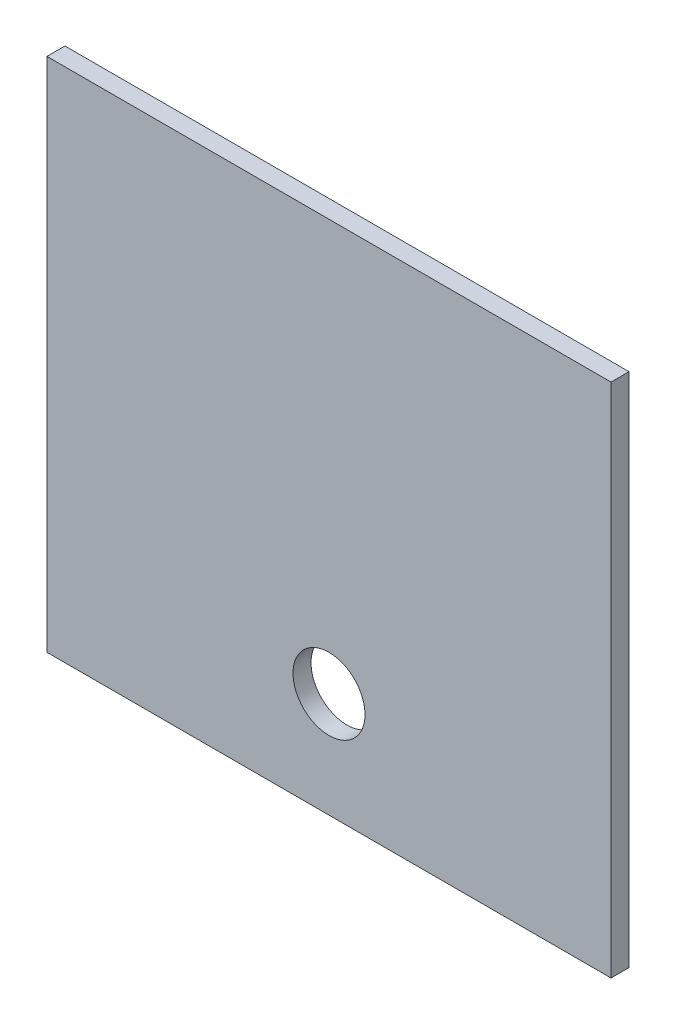
SolidWorks part; units mm, degrees
material "Oak"
ref_plane "Front Plane" through (0, 0, 0) normal (0, 0, 1) x (1, 0, 0)
ref_plane "Top Plane" through (0, 0, 0) normal (0, 1, 0) x (1, 0, 0)
ref_plane "Right Plane" through (0, 0, 0) normal (1, 0, 0) x (0, 0, -1)
sketch "Sketch1" plane through (0, 0, 0) normal (0, 0, 1) x (1, 0, 0)
  line L1 (-298.45, -152.4) -> (298.45, -152.4)
  line L2 (-298.45, -152.4) -> (-298.45, 152.4)
  line L3 (-298.45, 152.4) -> (298.45, 152.4)
  line L4 (298.45, -152.4) -> (298.45, 152.4)
  line L5 (-298.45, -152.4) -> (298.45, 152.4) construction
  line L6 (-298.45, 152.4) -> (298.45, -152.4) construction
  line L7 (-298.45, 158.75) -> (-298.45, 177.8) construction
  point P4 (0, 0)
  dimension "D2" = 304.8
extrude "Boss-Extrude1" add sketch "Sketch1" along normal blind 19.05
sketch "Sketch2" plane through (0, 152.4, 0) normal (0, 1, 0) x (1, 0, 0)
  line L4 (298.45, 0) -> (-298.45, 0)
  line L5 (-298.45, 0) -> (-298.45, -19.05)
  line L6 (-298.45, -19.05) -> (298.45, -19.05)
  line L7 (298.45, -19.05) -> (298.45, 0)
  line L8 (298.45, 0) -> (-298.45, 0)
  line L9 (-298.45, 0) -> (-298.45, -19.05)
  line L10 (-298.45, -19.05) -> (298.45, -19.05)
  line L11 (298.45, -19.05) -> (298.45, 0)
  dimension "D1" = 0
extrude "Boss-Extrude2" add sketch "Sketch2" along normal blind 25.4
sketch "Sketch3" plane through (0, -152.4, 0) normal (0, -1, 0) x (1, 0, 0)
  line L4 (-298.45, 0) -> (298.45, 0)
  line L5 (298.45, 0) -> (298.45, 19.05)
  line L6 (298.45, 19.05) -> (-298.45, 19.05)
  line L7 (-298.45, 19.05) -> (-298.45, 0)
  line L8 (-298.45, 0) -> (298.45, 0)
  line L9 (298.45, 0) -> (298.45, 19.05)
  line L10 (298.45, 19.05) -> (-298.45, 19.05)
  line L11 (-298.45, 19.05) -> (-298.45, 0)
  dimension "D1" = 0
extrude "Boss-Extrude3" add sketch "Sketch3" along normal blind 215.9
sketch "Sketch4" plane through (0, 0, 19.05) normal (0, 0, 1) x (1, 0, 0)
  line L0 (298.45, -368.3) -> (-298.45, -368.3) construction
  circle A0 centre (0, -257.175) radius 38.1
  circle A2 centre (0, -257.175) radius 25.4 construction
  dimension "D1" = 76.2
extrude "Cut-Extrude1" cut sketch "Sketch4" against normal through all
